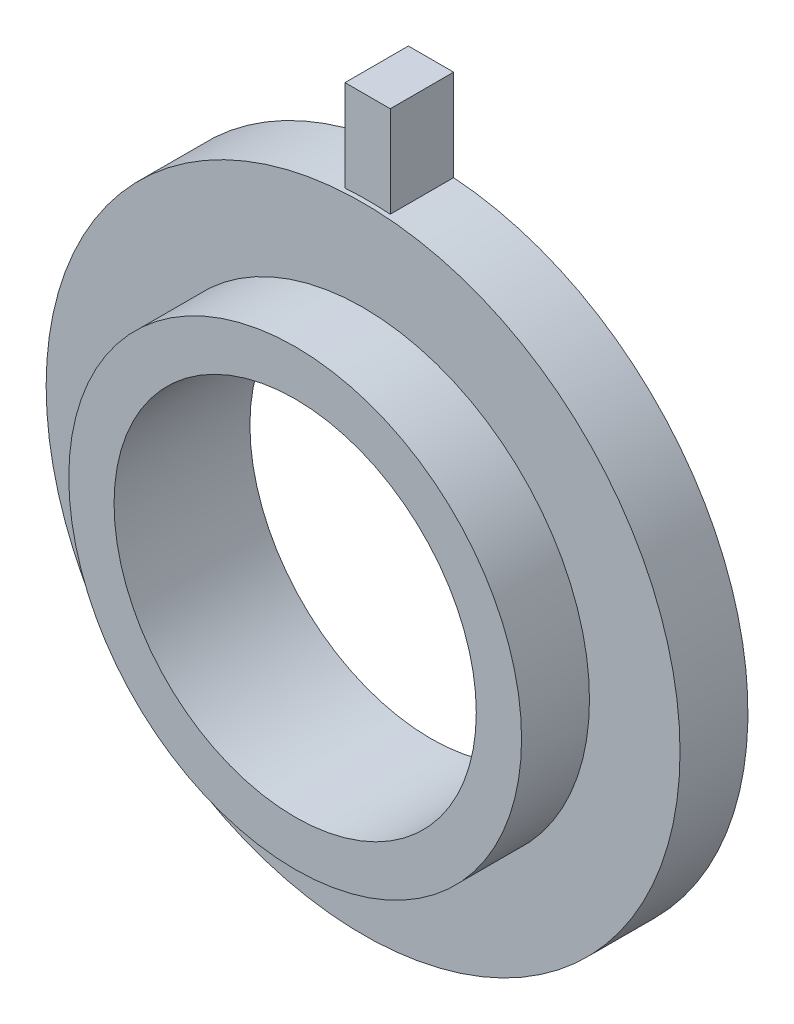
SolidWorks part; units mm, degrees
ref_plane "Front Plane" through (0, 0, 0) normal (0, 0, 1) x (1, 0, 0)
ref_plane "Top Plane" through (0, 0, 0) normal (0, 1, 0) x (1, 0, 0)
ref_plane "Right Plane" through (0, 0, 0) normal (1, 0, 0) x (0, 0, -1)
sketch "Sketch1" plane through (0, 0, 0) normal (0, 0, 1) x (1, 0, 0)
  circle A0 centre (0, 0) radius 20
  circle A1 centre (0, 0) radius 25
  dimension "D1" = 40
  dimension "D2" = 50
extrude "Boss-Extrude1" add sketch "Sketch1" along normal blind 15
sketch "Sketch2" plane through (0, 0, 0) normal (0, 0, -1) x (-1, 0, 0)
  circle A0 centre (0, 0) radius 35
  circle M1 centre (0, 0) radius 25
  dimension "D1" = 70
extrude "Boss-Extrude2" add sketch "Sketch2" against normal blind 7.5 contours A0 M1
sketch "Sketch3" plane through (0, 0, 0) normal (0, 0, 1) x (1, 0, 0)
  line L0 (0, 0) -> (0, 61.9889) construction
  line L1 (0, 35) -> (-35.5877, 35) construction
  line L2 (0, 35) -> (37.71, 35) construction
  line L4 (2.5, 45) -> (-2.5, 45)
  line L5 (2.5, 45) -> (2.5, 28.2056)
  line L6 (2.5, 28.2056) -> (-2.5, 28.2056)
  line L7 (-2.5, 45) -> (-2.5, 28.2056)
  circle A0 centre (0, 0) radius 35 construction
  dimension "D1" = 5
  dimension "D2" = 2.5
  dimension "D3" = 10
extrude "Boss-Extrude3" add sketch "Sketch3" along normal blind 7
